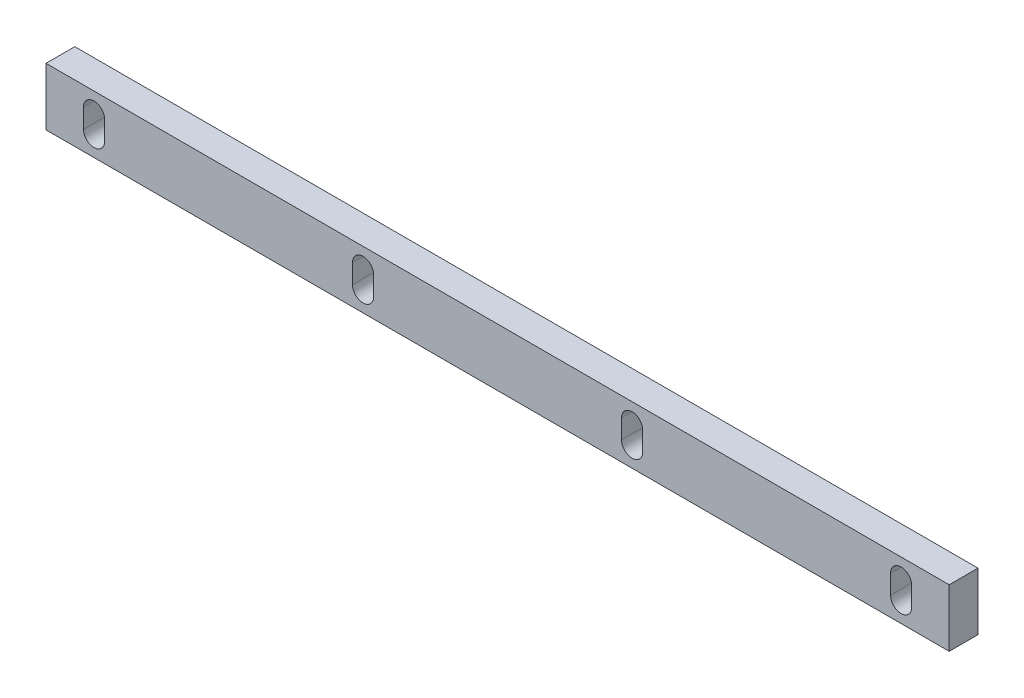
SolidWorks part; units mm, degrees
material "1.0038 (S235JRG2)"
ref_plane "Plan de face" through (0, 0, 0) normal (0, 0, 1) x (1, 0, 0)
ref_plane "Plan de dessus" through (0, 0, 0) normal (0, 1, 0) x (1, 0, 0)
ref_plane "Plan de droite" through (0, 0, 0) normal (1, 0, 0) x (0, 0, -1)
sketch "Esquisse1" plane through (0, 0, 0) normal (0, 0, 1) x (1, 0, 0)
  line L0 (-235, 0) -> (235, 0)
other "Elément mécano-soudé1"
ref_plane "Plan1" through (-235, 0, 0) normal (1, 0, 0) x (0, 1, 0)
sketch "plat" plane through (-235, 0, 0) normal (1, 0, 0) x (0, 1, 0)
  line L0 (-15, 0) -> (15, 0) construction
  line L1 (-15, 7.5) -> (15, 7.5)
  line L2 (-15, 7.5) -> (-15, -7.5)
  line L3 (-15, -7.5) -> (15, -7.5)
  line L4 (15, 7.5) -> (15, -7.5)
  line L5 (0, 7.5) -> (0, -7.5) construction
  point P8 (0, 0)
  dimension "B" = 30
  dimension "A" = 15
sketch "Esquisse7" plane through (0, 0, 7.5) normal (0, 0, 1) x (1, 0, 0)
  line L0 (-215.5, -5) -> (-215.5, 5)
  line L1 (-204.5, 5) -> (-204.5, -5)
  line L2 (235, 15) -> (-235, 15) construction
  line L3 (235, -15) -> (-235, -15) construction
  line L4 (-235, 15) -> (-235, -15) construction
  arc A0 (-215.5, 5) -> (-204.5, 5) centre (-210, 5) cw
  arc A1 (-204.5, -5) -> (-215.5, -5) centre (-210, -5) cw
  dimension "D1" = 11
  dimension "D2" = 10
  dimension "D3" = 10
  dimension "D4" = 25
extrude "Enlèv. mat.-Extru.2" cut sketch "Esquisse7" against normal blind 20
pattern_linear "Répétition linéaire1" count 4 spacing 140 along (1, 0, 0) of "Enlèv. mat.-Extru.2"
